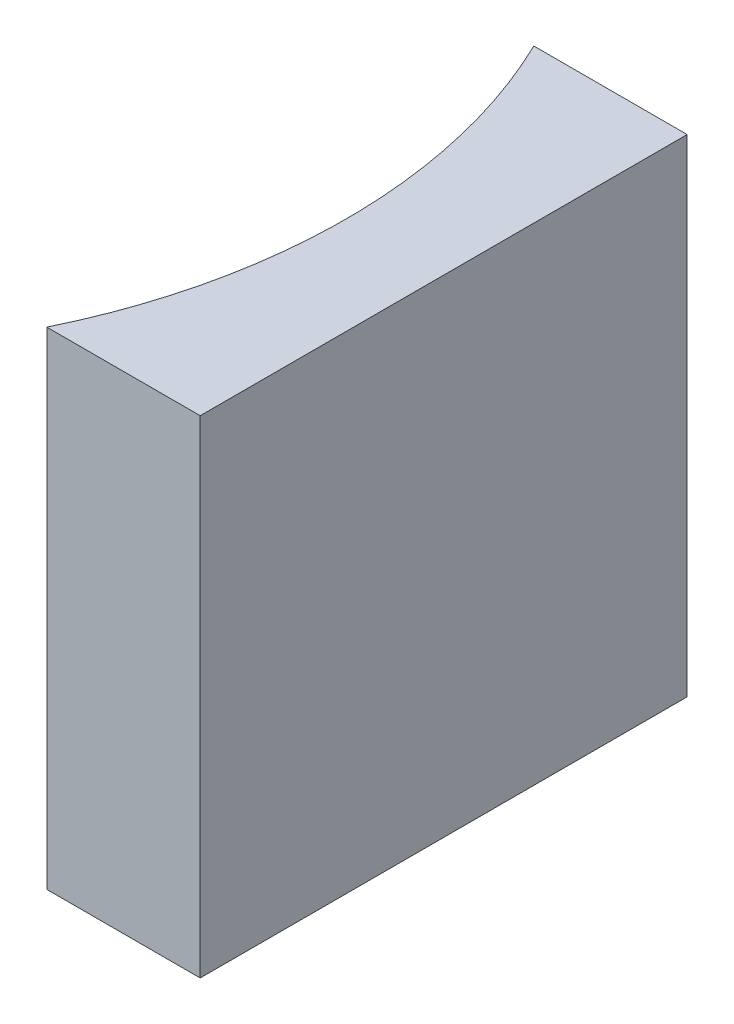
SolidWorks part; units mm, degrees
ref_plane "前视基准面" through (0, 0, 0) normal (0, 0, 1) x (1, 0, 0)
ref_plane "上视基准面" through (0, 0, 0) normal (0, 1, 0) x (1, 0, 0)
ref_plane "右视基准面" through (0, 0, 0) normal (1, 0, 0) x (0, 0, -1)
sketch "草图1" plane through (0, 0, 0) normal (0, 1, 0) x (1, 0, 0)
  line L0 (0, 0) -> (0, -10)
  line L1 (0, 0) -> (-3.1494, 0)
  line L2 (0, -10) -> (-3.1494, -10)
  line L3 (2.5782, -5) -> (-14.3559, -5) construction
  arc A0 (-3.1494, -10) -> (-3.1494, 0) centre (-13.45, -5) ccw
  point P7 (-2, -5)
  point P8 (0, -5)
  point P10 (5.335, -7.0959)
  point P11 (2.5782, -5)
  dimension "D2" = 11.45
  dimension "D3" = 2
  dimension "D1" = 10
extrude "凸台-拉伸1" add sketch "草图1" along normal blind 10
